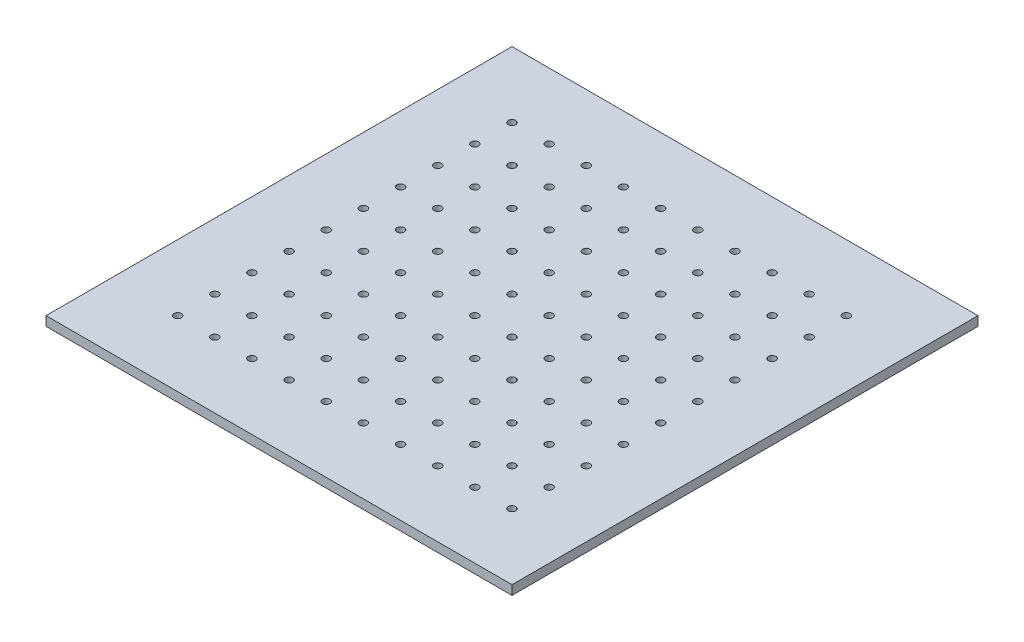
SolidWorks part; units mm, degrees
ref_plane "Front Plane" through (0, 0, 0) normal (0, 0, 1) x (1, 0, 0)
ref_plane "Top Plane" through (0, 0, 0) normal (0, 1, 0) x (1, 0, 0)
ref_plane "Right Plane" through (0, 0, 0) normal (1, 0, 0) x (0, 0, -1)
sketch "Sketch1" plane through (0, 0, 0) normal (0, 1, 0) x (1, 0, 0)
  line L0 (0, 0) -> (0, -45) construction
  line L1 (-45, 273.6) -> (273.6, 273.6)
  line L2 (-45, 273.6) -> (-45, -45)
  line L3 (-45, -45) -> (273.6, -45)
  line L4 (273.6, 273.6) -> (273.6, -45)
  line L6 (-45, 0) -> (0, 0) construction
  circle A0 centre (0, 0) radius 2.5527
  circle A1 centre (25.4, 0) radius 2.5527
  circle A2 centre (50.8, 0) radius 2.5527
  circle A3 centre (76.2, 0) radius 2.5527
  circle A4 centre (101.6, 0) radius 2.5527
  circle A5 centre (127, 0) radius 2.5527
  circle A6 centre (152.4, 0) radius 2.5527
  circle A7 centre (177.8, 0) radius 2.5527
  circle A8 centre (203.2, 0) radius 2.5527
  circle A9 centre (228.6, 0) radius 2.5527
  circle A10 centre (0, 25.4) radius 2.5527
  circle A11 centre (25.4, 25.4) radius 2.5527
  circle A12 centre (50.8, 25.4) radius 2.5527
  circle A13 centre (76.2, 25.4) radius 2.5527
  circle A14 centre (101.6, 25.4) radius 2.5527
  circle A15 centre (127, 25.4) radius 2.5527
  circle A16 centre (152.4, 25.4) radius 2.5527
  circle A17 centre (177.8, 25.4) radius 2.5527
  circle A18 centre (203.2, 25.4) radius 2.5527
  circle A19 centre (228.6, 25.4) radius 2.5527
  circle A20 centre (0, 50.8) radius 2.5527
  circle A21 centre (25.4, 50.8) radius 2.5527
  circle A22 centre (50.8, 50.8) radius 2.5527
  circle A23 centre (76.2, 50.8) radius 2.5527
  circle A24 centre (101.6, 50.8) radius 2.5527
  circle A25 centre (127, 50.8) radius 2.5527
  circle A26 centre (152.4, 50.8) radius 2.5527
  circle A27 centre (177.8, 50.8) radius 2.5527
  circle A28 centre (203.2, 50.8) radius 2.5527
  circle A29 centre (228.6, 50.8) radius 2.5527
  circle A30 centre (0, 76.2) radius 2.5527
  circle A31 centre (25.4, 76.2) radius 2.5527
  circle A32 centre (50.8, 76.2) radius 2.5527
  circle A33 centre (76.2, 76.2) radius 2.5527
  circle A34 centre (101.6, 76.2) radius 2.5527
  circle A35 centre (127, 76.2) radius 2.5527
  circle A36 centre (152.4, 76.2) radius 2.5527
  circle A37 centre (177.8, 76.2) radius 2.5527
  circle A38 centre (203.2, 76.2) radius 2.5527
  circle A39 centre (228.6, 76.2) radius 2.5527
  circle A40 centre (0, 101.6) radius 2.5527
  circle A41 centre (25.4, 101.6) radius 2.5527
  circle A42 centre (50.8, 101.6) radius 2.5527
  circle A43 centre (76.2, 101.6) radius 2.5527
  circle A44 centre (101.6, 101.6) radius 2.5527
  circle A45 centre (127, 101.6) radius 2.5527
  circle A46 centre (152.4, 101.6) radius 2.5527
  circle A47 centre (177.8, 101.6) radius 2.5527
  circle A48 centre (203.2, 101.6) radius 2.5527
  circle A49 centre (228.6, 101.6) radius 2.5527
  circle A50 centre (0, 127) radius 2.5527
  circle A51 centre (25.4, 127) radius 2.5527
  circle A52 centre (50.8, 127) radius 2.5527
  circle A53 centre (76.2, 127) radius 2.5527
  circle A54 centre (101.6, 127) radius 2.5527
  circle A55 centre (127, 127) radius 2.5527
  circle A56 centre (152.4, 127) radius 2.5527
  circle A57 centre (177.8, 127) radius 2.5527
  circle A58 centre (203.2, 127) radius 2.5527
  circle A59 centre (228.6, 127) radius 2.5527
  circle A60 centre (0, 152.4) radius 2.5527
  circle A61 centre (25.4, 152.4) radius 2.5527
  circle A62 centre (50.8, 152.4) radius 2.5527
  circle A63 centre (76.2, 152.4) radius 2.5527
  circle A64 centre (101.6, 152.4) radius 2.5527
  circle A65 centre (127, 152.4) radius 2.5527
  circle A66 centre (152.4, 152.4) radius 2.5527
  circle A67 centre (177.8, 152.4) radius 2.5527
  circle A68 centre (203.2, 152.4) radius 2.5527
  circle A69 centre (228.6, 152.4) radius 2.5527
  circle A70 centre (0, 177.8) radius 2.5527
  circle A71 centre (25.4, 177.8) radius 2.5527
  circle A72 centre (50.8, 177.8) radius 2.5527
  circle A73 centre (76.2, 177.8) radius 2.5527
  circle A74 centre (101.6, 177.8) radius 2.5527
  circle A75 centre (127, 177.8) radius 2.5527
  circle A76 centre (152.4, 177.8) radius 2.5527
  circle A77 centre (177.8, 177.8) radius 2.5527
  circle A78 centre (203.2, 177.8) radius 2.5527
  circle A79 centre (228.6, 177.8) radius 2.5527
  circle A80 centre (0, 203.2) radius 2.5527
  circle A81 centre (25.4, 203.2) radius 2.5527
  circle A82 centre (50.8, 203.2) radius 2.5527
  circle A83 centre (76.2, 203.2) radius 2.5527
  circle A84 centre (101.6, 203.2) radius 2.5527
  circle A85 centre (127, 203.2) radius 2.5527
  circle A86 centre (152.4, 203.2) radius 2.5527
  circle A87 centre (177.8, 203.2) radius 2.5527
  circle A88 centre (203.2, 203.2) radius 2.5527
  circle A89 centre (228.6, 203.2) radius 2.5527
  circle A90 centre (0, 228.6) radius 2.5527
  circle A91 centre (25.4, 228.6) radius 2.5527
  circle A92 centre (50.8, 228.6) radius 2.5527
  circle A93 centre (76.2, 228.6) radius 2.5527
  circle A94 centre (101.6, 228.6) radius 2.5527
  circle A95 centre (127, 228.6) radius 2.5527
  circle A96 centre (152.4, 228.6) radius 2.5527
  circle A97 centre (177.8, 228.6) radius 2.5527
  circle A98 centre (203.2, 228.6) radius 2.5527
  circle A99 centre (228.6, 228.6) radius 2.5527
  dimension "D1" = 10
  dimension "D2" = 10
extrude "Boss-Extrude1" add sketch "Sketch1" along normal blind 6.35
